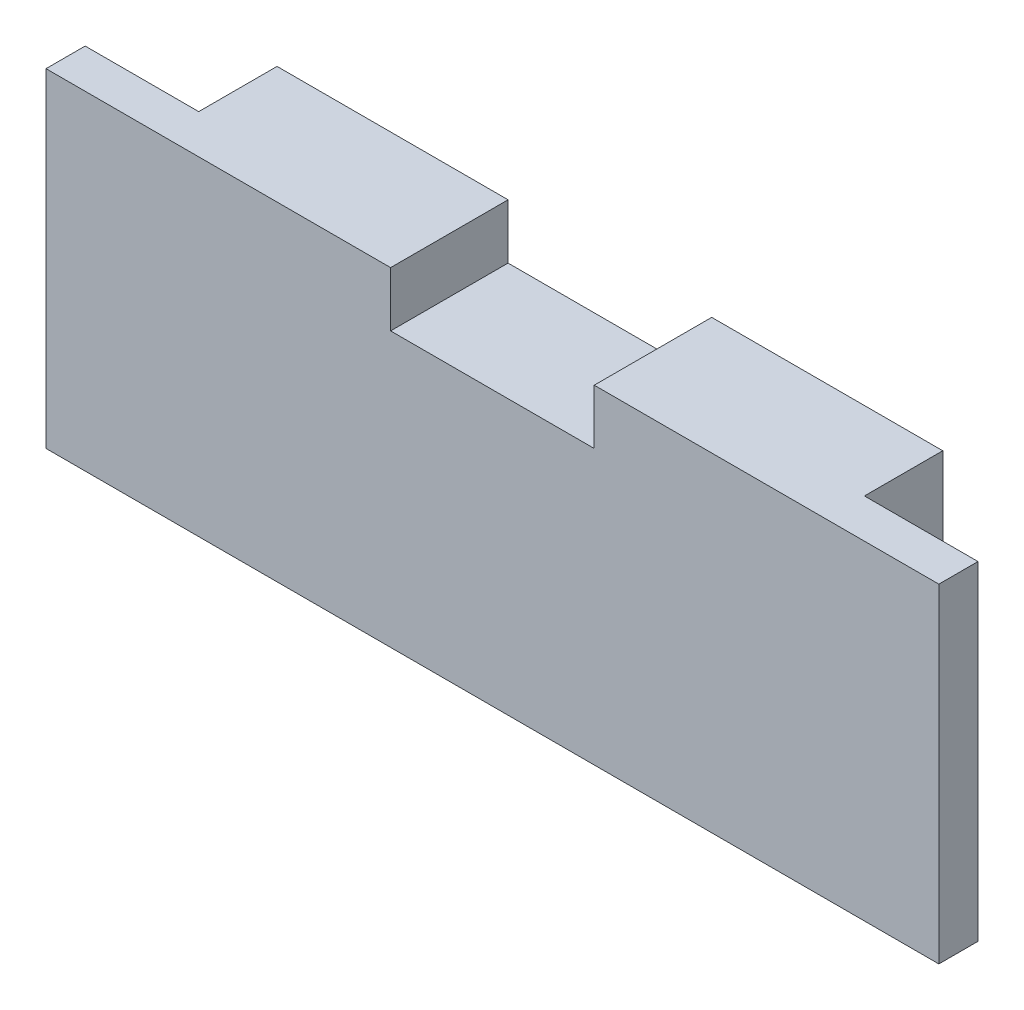
SolidWorks part; units mm, degrees
material "ABS"
ref_plane "Plan de face" through (0, 0, 0) normal (0, 0, 1) x (1, 0, 0)
ref_plane "Plan de dessus" through (0, 0, 0) normal (0, 1, 0) x (1, 0, 0)
ref_plane "Plan de droite" through (0, 0, 0) normal (1, 0, 0) x (0, 0, -1)
sketch "Sketch1" plane through (0, 0, 0) normal (0, 0, 1) x (1, 0, 0)
  line L1 (-28.5, -10.5) -> (28.5, -10.5)
  line L2 (-28.5, -10.5) -> (-28.5, 10.5)
  line L3 (-28.5, 10.5) -> (28.5, 10.5)
  line L4 (28.5, -10.5) -> (28.5, 10.5)
  line L5 (-28.5, -10.5) -> (28.5, 10.5) construction
  line L6 (-28.5, 10.5) -> (28.5, -10.5) construction
  point P0 (0, 0)
  dimension "D1" = 57
  dimension "D2" = 21
extrude "Boss-Extrude1" add sketch "Sketch1" along normal blind 2.5
sketch "Sketch2" plane through (0, 0, 0) normal (0, 0, -1) x (-1, 0, 0)
  line L0 (-28.5, 10.5) -> (28.5, 10.5) construction
  line L1 (-21.25, -10.5) -> (21.25, -10.5)
  line L2 (-21.25, -10.5) -> (-21.25, 10.5)
  line L3 (-21.25, 10.5) -> (21.25, 10.5)
  line L4 (21.25, -10.5) -> (21.25, 10.5)
  line L5 (-21.25, -10.5) -> (21.25, 10.5) construction
  line L6 (-21.25, 10.5) -> (21.25, -10.5) construction
  point P0 (0, 0)
  dimension "D1" = 42.5
extrude "Boss-Extrude2" add sketch "Sketch2" along normal blind 5
sketch "Sketch3" plane through (0, 0, 2.5) normal (0, 0, 1) x (1, 0, 0)
  line L0 (28.5, 10.5) -> (-28.5, 10.5) construction
  line L1 (-6.5, 7) -> (6.5, 7)
  line L2 (-6.5, 7) -> (-6.5, 10.5)
  line L3 (-6.5, 10.5) -> (6.5, 10.5)
  line L4 (6.5, 7) -> (6.5, 10.5)
  line L5 (-6.5, 7) -> (6.5, 10.5) construction
  line L6 (-6.5, 10.5) -> (6.5, 7) construction
  point P0 (0, 8.75)
  point P7 (0, 0)
  dimension "D1" = 13
  dimension "D2" = 3.5
extrude "Cut-Extrude1" cut sketch "Sketch3" against normal through all
